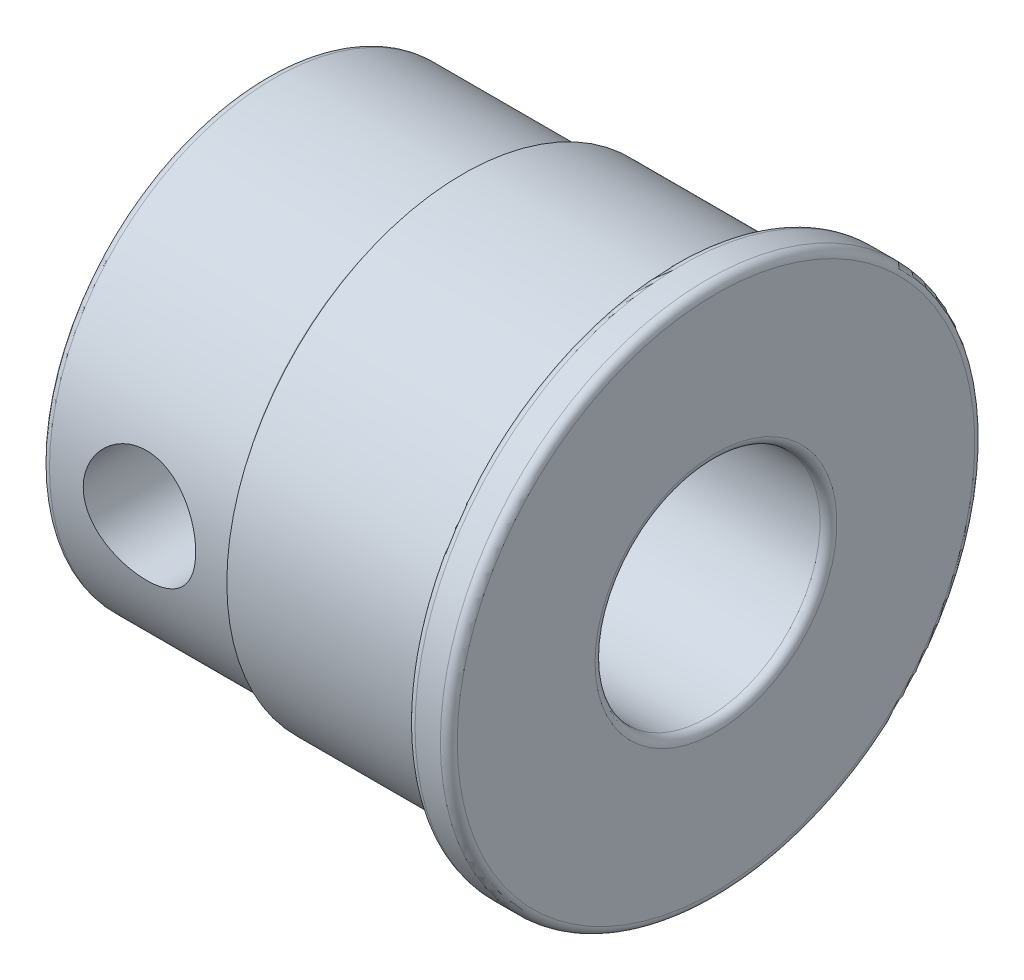
SolidWorks part; units mm, degrees
ref_plane "Front Plane" through (0, 0, 0) normal (0, 0, 1) x (1, 0, 0)
ref_plane "Top Plane" through (0, 0, 0) normal (0, 1, 0) x (1, 0, 0)
ref_plane "Right Plane" through (0, 0, 0) normal (1, 0, 0) x (0, 0, -1)
sketch "Sketch1" plane through (0, 0, 0) normal (0, 1, 0) x (1, 0, 0)
  line L0 (0, 0) -> (0, 4) construction
  line L1 (0, 4) -> (0, 8)
  line L2 (0, 8) -> (7, 8)
  line L3 (7, 8) -> (7, 8.3938)
  line L4 (7, 8.3938) -> (14.5, 8.3938)
  line L5 (14.5, 8.3938) -> (14.5, 9.5)
  line L6 (14.5, 9.5) -> (16, 9.5)
  line L7 (16, 9.5) -> (16, 4)
  line L8 (16, 4) -> (0, 4)
  line L9 (0, 0) -> (19.664, 0) construction
  dimension "D1" = 16
  dimension "2.5" = 4
  dimension "D2" = 8
  dimension "D3" = 1.5
  dimension "D4" = 7.5
  dimension "D5" = 7
revolve "Revolve1" add sketch "Sketch1" angle 360 about L9
fillet "Fillet1" radius 0.3 6 edges at (7, 0, 8) (0, 0, 8) (16, 0, 9.5) (14.5, 0, 9.5) (0, 0, 4) (16, 0, 4)
sketch "Sketch2" plane through (0, 0, 0) normal (0, 0, 1) x (1, 0, 0)
  line L0 (0, 0) -> (7, 0) construction
  line L1 (7, 8.3938) -> (7, -8.3938) construction
  circle A0 centre (3.5, 0) radius 2
  dimension "D1" = 4
extrude "Cut-Extrude1" cut sketch "Sketch2" against normal through all both and the other way through all
